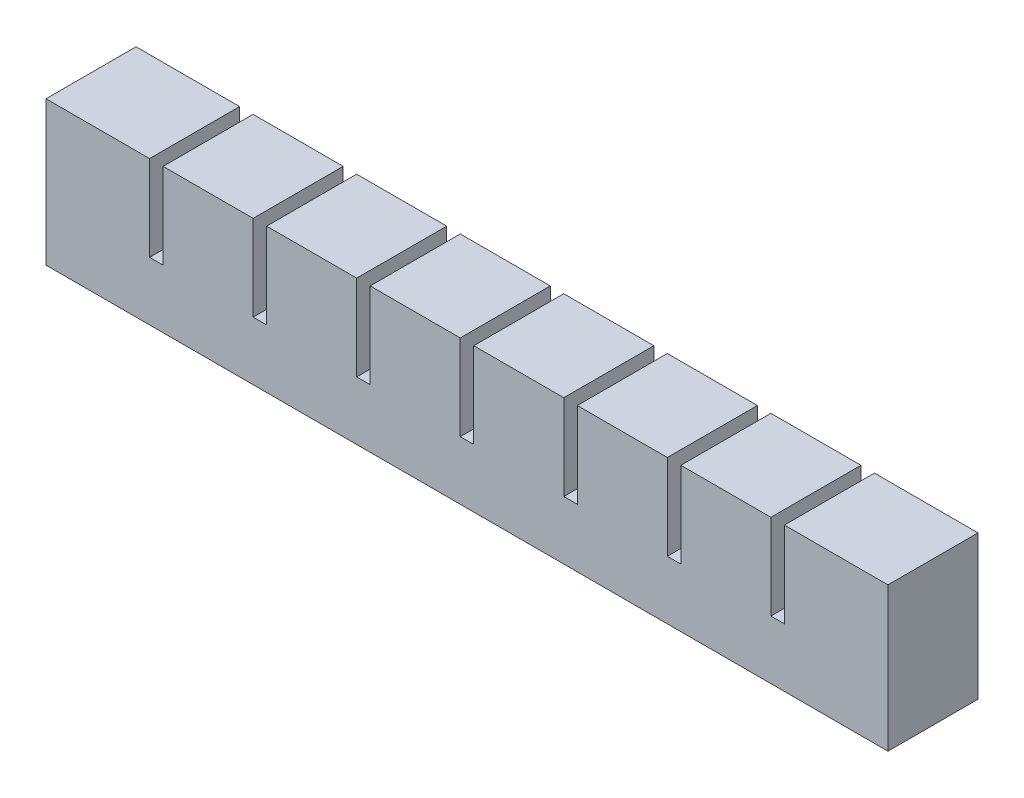
SolidWorks part; units mm, degrees
ref_plane "Front Plane" through (0, 0, 0) normal (0, 0, 1) x (1, 0, 0)
ref_plane "Top Plane" through (0, 0, 0) normal (0, 1, 0) x (1, 0, 0)
ref_plane "Right Plane" through (0, 0, 0) normal (1, 0, 0) x (0, 0, -1)
sketch "Sketch1" plane through (0, 0, 0) normal (0, 0, 1) x (1, 0, 0)
  line L1 (0, 0) -> (20, 0)
  line L2 (0, 0) -> (0, 25)
  line L3 (0, 25) -> (20, 25)
  line L4 (20, 0) -> (20, 25)
  dimension "D1" = 20
  dimension "D2" = 25
extrude "Boss-Extrude1" add sketch "Sketch1" along normal blind 20
sketch "Sketch2" plane through (0, 0, 0) normal (0, -1, 0) x (1, 0, 0)
  line L0 (20, 20) -> (20, 0) construction
  line L1 (6, 14) -> (14, 14)
  line L2 (6, 14) -> (6, 6)
  line L3 (6, 6) -> (14, 6)
  line L4 (14, 14) -> (14, 6)
  line L5 (0, 20) -> (0, 0) construction
  line L6 (0, 20) -> (20, 20) construction
  line L7 (0, 0) -> (20, 0) construction
  dimension "D1" = 6
  dimension "D2" = 6
  dimension "D3" = 6
  dimension "D4" = 6
extrude "Cut-Extrude1" cut sketch "Sketch2" against normal blind 20
sketch "Sketch3" plane through (20, 0, 0) normal (1, 0, 0) x (0, 0, -1)
  line L0 (0, 0) -> (0, 25) construction
  line L1 (-20, 0) -> (0, 0)
  line L2 (-20, 0) -> (-20, 6)
  line L3 (-20, 6) -> (0, 6)
  line L4 (0, 0) -> (0, 6)
  dimension "D1" = 6
extrude "Boss-Extrude2" add sketch "Sketch3" along normal blind 3
pattern_linear "LPattern1" count 8 spacing 23 along (1, 0, 0) of bodies 103
combine bodies "Combine1" operation type add bodies to combine 104 105 106 103 107 108 109 110
sketch "Sketch4" plane through (181, 0, 0) normal (1, 0, 0) x (0, 0, -1)
  line L1 (-20, 25) -> (0, 25)
  line L2 (-20, 25) -> (-20, 6)
  line L3 (-20, 6) -> (0, 6)
  line L4 (0, 25) -> (0, 6)
extrude "Boss-Extrude3" add sketch "Sketch4" along normal up to surface (3 mm away) up to face at (184, 3, 10)
sketch "Sketch5" plane through (0, 0, 0) normal (-1, 0, 0) x (0, 0, 1)
  line L1 (0, 0) -> (20, 0)
  line L2 (0, 0) -> (0, 25)
  line L3 (0, 25) -> (20, 25)
  line L4 (20, 0) -> (20, 25)
extrude "Boss-Extrude4" add sketch "Sketch5" along normal blind 3
ref_point "Point1"
sketch "Sketch6" plane through (0, 0, 0) normal (0, -1, 0) x (1, 0, 0)
  line L0 (167, 14) -> (167, 6) construction
  line L1 (14, 11) -> (167, 11)
  line L2 (14, 11) -> (14, 9)
  line L3 (14, 9) -> (167, 9)
  line L4 (167, 11) -> (167, 9)
  line L5 (14, 11) -> (167, 9) construction
  line L6 (14, 9) -> (167, 11) construction
  point P0 (90.5, 10)
  dimension "D1" = 2
extrude "Cut-Extrude2" cut sketch "Sketch6" against normal blind 2
sketch "Sketch7" plane through (0, 0, 0) normal (0, -1, 0) x (1, 0, 0)
  line L0 (184, 20) -> (184, 0) construction
  line L1 (-3, 20) -> (184, 20)
  line L2 (-3, 20) -> (-3, 0)
  line L3 (-3, 0) -> (184, 0)
  line L4 (184, 20) -> (184, 0)
extrude "Boss-Extrude5" add sketch "Sketch7" along normal blind 7
